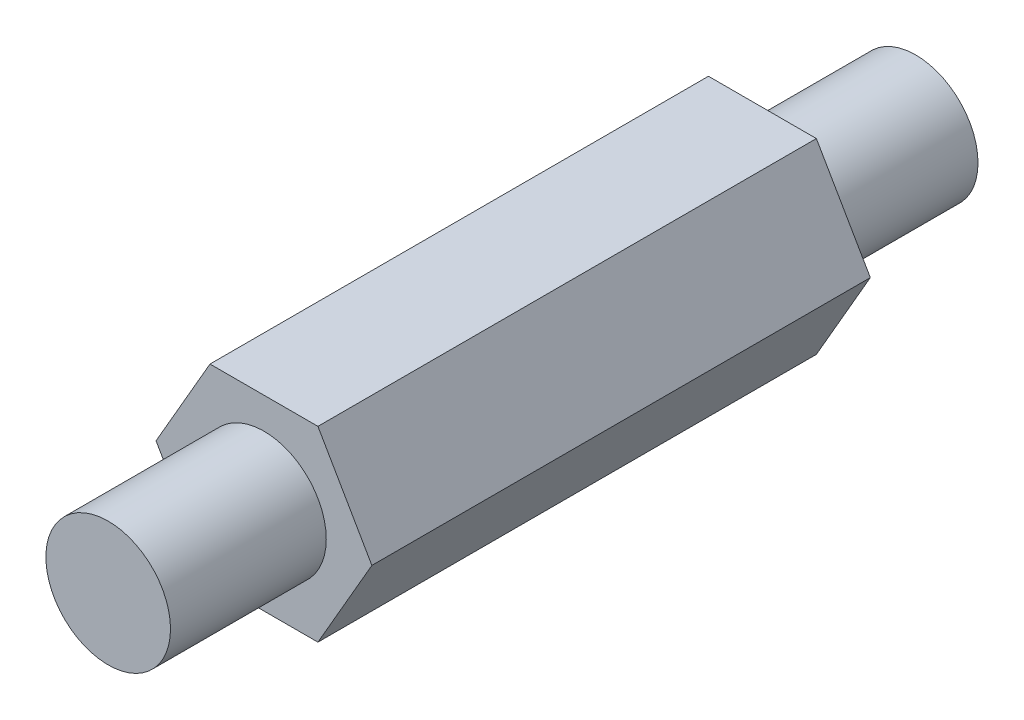
SolidWorks part; units mm, degrees
ref_plane "Front Plane" through (0, 0, 0) normal (0, 0, 1) x (1, 0, 0)
ref_plane "Top Plane" through (0, 0, 0) normal (0, 1, 0) x (1, 0, 0)
ref_plane "Right Plane" through (0, 0, 0) normal (1, 0, 0) x (0, 0, -1)
sketch "Sketch1" plane through (0, 0, 0) normal (0, 0, 1) x (1, 0, 0)
  line L1 (-2.7496, -4.7625) -> (2.7496, -4.7625)
  line L2 (2.7496, -4.7625) -> (5.4993, 0)
  line L3 (5.4993, 0) -> (2.7496, 4.7625)
  line L4 (2.7496, 4.7625) -> (-2.7496, 4.7625)
  line L5 (-2.7496, 4.7625) -> (-5.4993, 0)
  line L6 (-5.4993, 0) -> (-2.7496, -4.7625)
  circle A0 centre (0, 0) radius 4.7625 construction
  dimension "D1" = 9.525
extrude "Boss-Extrude1" add sketch "Sketch1" along normal blind 41.148
sketch "Sketch2" plane through (0, 0, 41.148) normal (0, 0, 1) x (1, 0, 0)
  circle A0 centre (0, 0) radius 3.175
  dimension "D1" = 6.35
extrude "Cut-Extrude1" cut sketch "Sketch2" against normal blind 7.9375 flip side to cut
ref_plane "Plane1" through (0, 0, 7.8105) normal (0, 0, 1) x (1, 0, 0)
sketch "Sketch3" plane through (0, 0, 7.8105) normal (0, 0, 1) x (1, 0, 0)
  circle A0 centre (0, 0) radius 3.175
  circle A1 centre (0, 0) radius 3.175 construction
extrude "Cut-Extrude2" cut sketch "Sketch3" against normal through all flip side to cut
